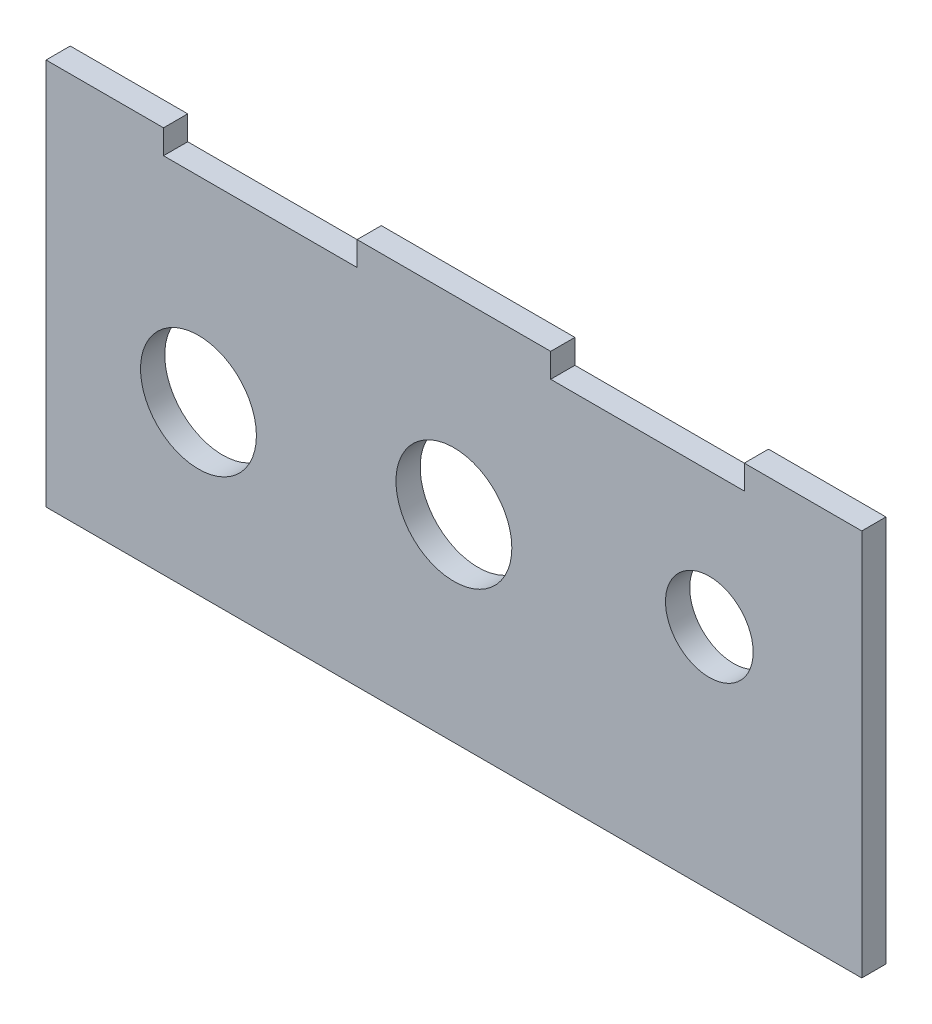
SolidWorks part; units mm, degrees
ref_plane "Front Plane" through (0, 0, 0) normal (0, 0, 1) x (1, 0, 0)
ref_plane "Top Plane" through (0, 0, 0) normal (0, 1, 0) x (1, 0, 0)
ref_plane "Right Plane" through (0, 0, 0) normal (1, 0, 0) x (0, 0, -1)
sketch "Sketch1" plane through (0, 0, 0) normal (0, 0, 1) x (1, 0, 0)
  line L0 (40.8129, 47.625) -> (66.2129, 47.625) construction
  line L1 (0, 0) -> (107.0257, 0)
  line L2 (0, 0) -> (0, 50.8)
  line L3 (0, 50.8) -> (107.0257, 50.8)
  line L4 (107.0257, 0) -> (107.0257, 50.8)
  line L5 (15.4129, 50.8) -> (40.8129, 50.8)
  line L6 (15.4129, 50.8) -> (15.4129, 47.625)
  line L7 (15.4129, 47.625) -> (40.8129, 47.625)
  line L8 (40.8129, 50.8) -> (40.8129, 47.625)
  line L9 (66.2129, 50.8) -> (91.6129, 50.8)
  line L10 (66.2129, 50.8) -> (66.2129, 47.625)
  line L11 (66.2129, 47.625) -> (91.6129, 47.625)
  line L12 (91.6129, 50.8) -> (91.6129, 47.625)
  circle A0 centre (20, 21.9125) radius 7.6
  circle A1 centre (53.5129, 25.9063) radius 7.6
  circle A2 centre (87.0257, 29.9) radius 5.75
  point P19 (53.5129, 47.625)
  point P20 (53.5129, 0)
  point P22 (20, 21.9125)
  dimension "D4" = 15.2
  dimension "D5" = 11.5
  dimension "D1" = 21.9125
  dimension "D2" = 25.9063
  dimension "D3" = 29.9
  dimension "D6" = 50.8
  dimension "D7" = 20
  dimension "D8" = 20
  dimension "D9" = 33.75
  dimension "D10" = 33.75
  dimension "D11" = 25.4
  dimension "D12" = 3.175
extrude "Boss-Extrude1" add sketch "Sketch1" along normal blind 3.175 contours L0 L7 L6 L3 L2 L1 L4 L12 L11 A2 A1 A0 | L8 L0 L10 L3
